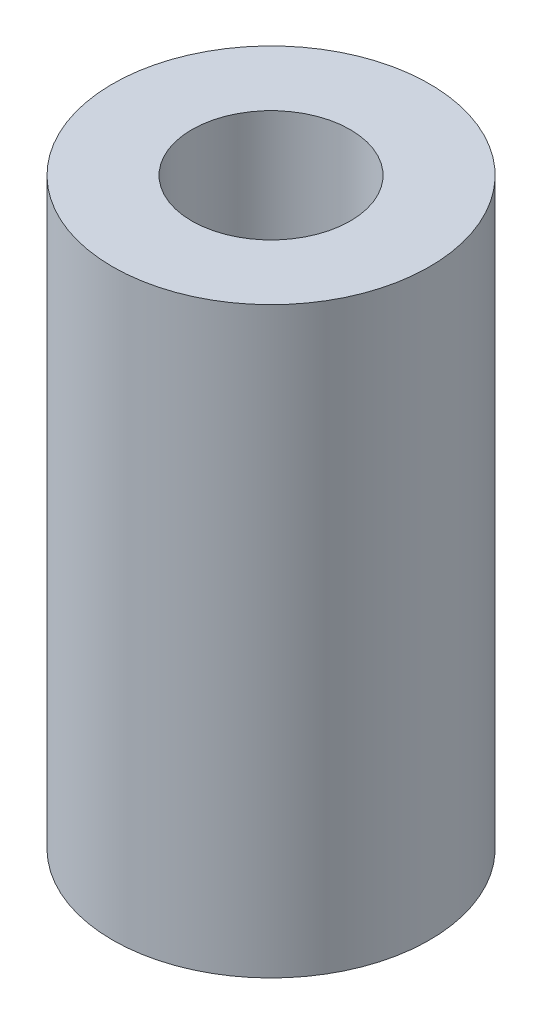
SolidWorks part; units mm, degrees
material "6061-T6 (SS)"
ref_plane "Front Plane" through (0, 0, 0) normal (0, 0, 1) x (1, 0, 0)
ref_plane "Top Plane" through (0, 0, 0) normal (0, 1, 0) x (1, 0, 0)
ref_plane "Right Plane" through (0, 0, 0) normal (1, 0, 0) x (0, 0, -1)
sketch "Sketch1" plane through (0, 0, 0) normal (0, 1, 0) x (1, 0, 0)
  circle A0 centre (0, 0) radius 6.35
  circle A1 centre (0, 0) radius 3.175
  dimension "D1" = 12.7
  dimension "D2" = 6.35
extrude "Boss-Extrude1" add sketch "Sketch1" along normal blind 23.368
